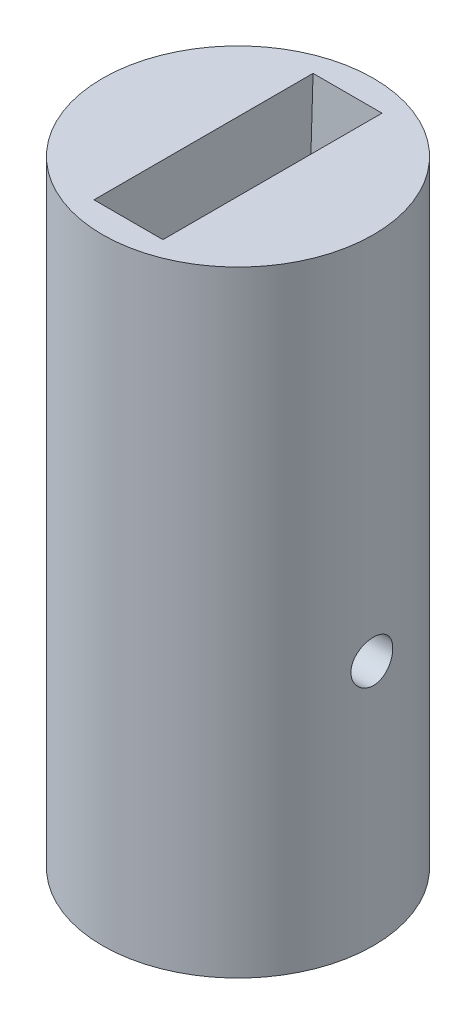
SolidWorks part; units mm, degrees
material "ABS"
ref_plane "Front Plane" through (0, 0, 0) normal (0, 0, 1) x (1, 0, 0)
ref_plane "Top Plane" through (0, 0, 0) normal (0, 1, 0) x (1, 0, 0)
ref_plane "Right Plane" through (0, 0, 0) normal (1, 0, 0) x (0, 0, -1)
sketch "Sketch1" plane through (0, 0, 0) normal (1, 0, 0) x (0, 0, -1)
  line L0 (0, 0) -> (0, -380) construction
  line L1 (-7.5, -380) -> (7.5, -380)
  line L2 (7.5, -380) -> (17.5, -57.3912)
  line L3 (-7.5, -380) -> (-17.5, -57.3912)
  circle A0 centre (0, 0) radius 60
  circle A1 centre (0, -365) radius 2.5 construction
  point P7 (0, -380)
  dimension "D2" = 120
  dimension "D5" = 5
  dimension "D6" = 15
  dimension "D1" = 380
  dimension "D3" = 15
  dimension "D4" = 35
sketch "Sketch2" plane through (0, 0, 0) normal (1, 0, 0) x (0, 0, -1)
  line L0 (0, -385) -> (11, -385)
  line L1 (11, -385) -> (11, -335)
  line L4 (11, -335) -> (0, -335)
  line L5 (0, 0) -> (0, -380) construction
  line L6 (0, -335) -> (0, -385)
  line L7 (-7.5, -380) -> (7.5, -380) construction
  line L8 (0, -385) -> (0, 0) construction
  dimension "D1" = 5
  dimension "D2" = 22
  dimension "D3" = 50
revolve "Revolve1" add sketch "Sketch2" angle 360 about L8
extrude "Cut-Extrude1" cut sketch "Sketch1" against normal mid plane 5.6 contours A0 L0 L1 L2 | L0 A0 L3 L1
sketch "Sketch3" plane through (0, 0, 0) normal (1, 0, 0) x (0, 0, -1)
  point P0 (0, -365)
hole_wizard "M3 Clearance Hole1" positions "Sketch3" profile "Sketch4" hole size "M3" standard "ANSI Metric"
sketch "Sketch4" plane through (0, -365, 0) normal (0, 1, 0) x (0, 0, 1)
  line L0 (0, 0) -> (0, 11)
  line L1 (0, 11) -> (1.7, 11)
  line L2 (1.7, 11) -> (1.7, 0.021)
  line L3 (1.7, 0.021) -> (1.725, 0)
  line L5 (1.725, 0) -> (0, 0)
  line L6 (-1.7, 0.021) -> (-1.725, 0) construction
  line L11 (0, -6.35) -> (0, 107.95) construction
  dimension "Thru Hole Dia." = 3.4
  dimension "Thru Hole Depth" = 11
  dimension "Near C'Sink Dia." = 3.45
  dimension "Near C'Sink Angle" = 100
mirror "Mirror1" about plane through (0, 0, 0) normal (1, 0, 0) of "M3 Clearance Hole1"
